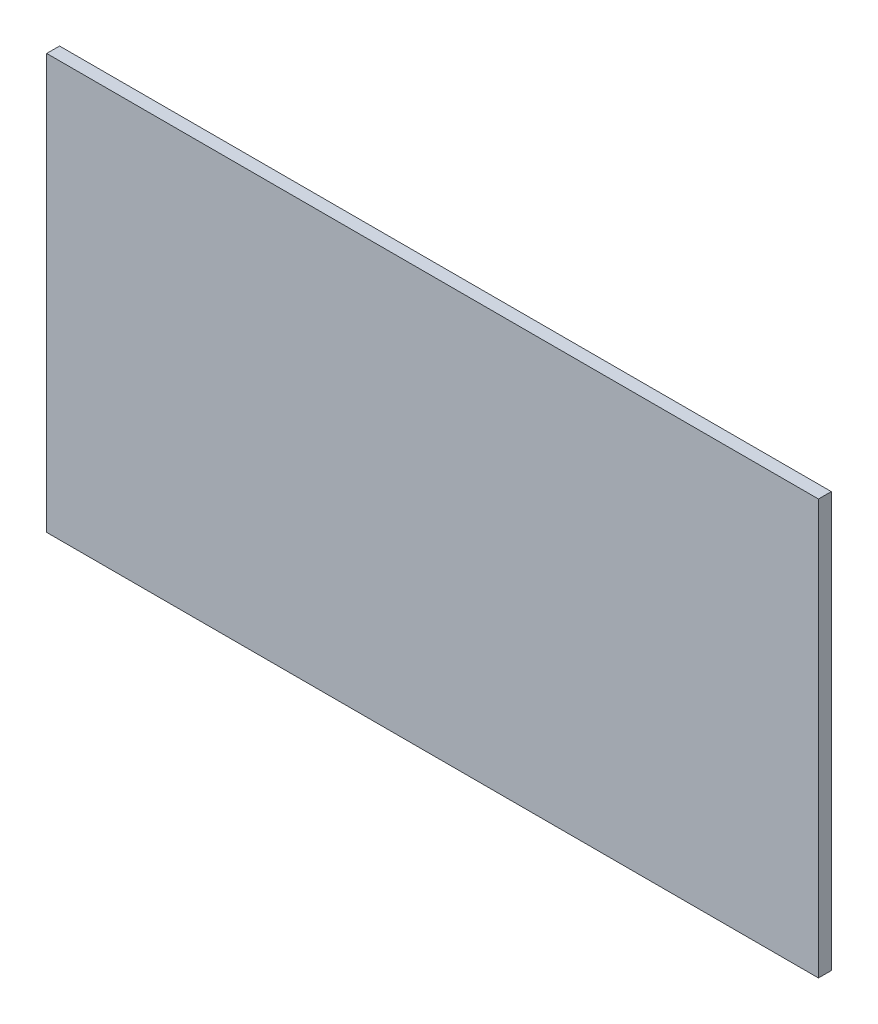
SolidWorks part; units mm, degrees
ref_plane "Alzado" through (0, 0, 0) normal (0, 0, 1) x (1, 0, 0)
ref_plane "Planta" through (0, 0, 0) normal (0, 1, 0) x (1, 0, 0)
ref_plane "Vista lateral" through (0, 0, 0) normal (1, 0, 0) x (0, 0, -1)
sketch "Croquis1" plane through (0, 0, 0) normal (0, 0, 1) x (1, 0, 0)
  line L1 (-71.2686, 22.3939) -> (1128.7314, 22.3939)
  line L2 (-71.2686, 22.3939) -> (-71.2686, -622.6061)
  line L3 (-71.2686, -622.6061) -> (1128.7314, -622.6061)
  line L4 (1128.7314, 22.3939) -> (1128.7314, -622.6061)
  dimension "D1" = 1200
  dimension "D2" = 645
extrude "Saliente-Extruir1" add sketch "Croquis1" along normal blind 20
